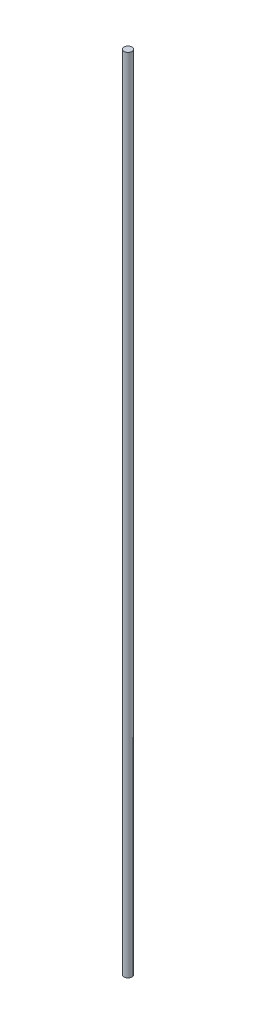
SolidWorks part; units mm, degrees
material "6063-T6"
ref_plane "Alzado" through (0, 0, 0) normal (0, 0, 1) x (1, 0, 0)
ref_plane "Planta" through (0, 0, 0) normal (0, 1, 0) x (1, 0, 0)
ref_plane "Vista lateral" through (0, 0, 0) normal (1, 0, 0) x (0, 0, -1)
sketch "Croquis1" plane through (0, 0, 0) normal (0, 1, 0) x (1, 0, 0)
  circle A0 centre (0, 0) radius 2.1
  dimension "D1" = 4.2
extrude "Saliente-Extruir1" add sketch "Croquis1" along normal blind 429
